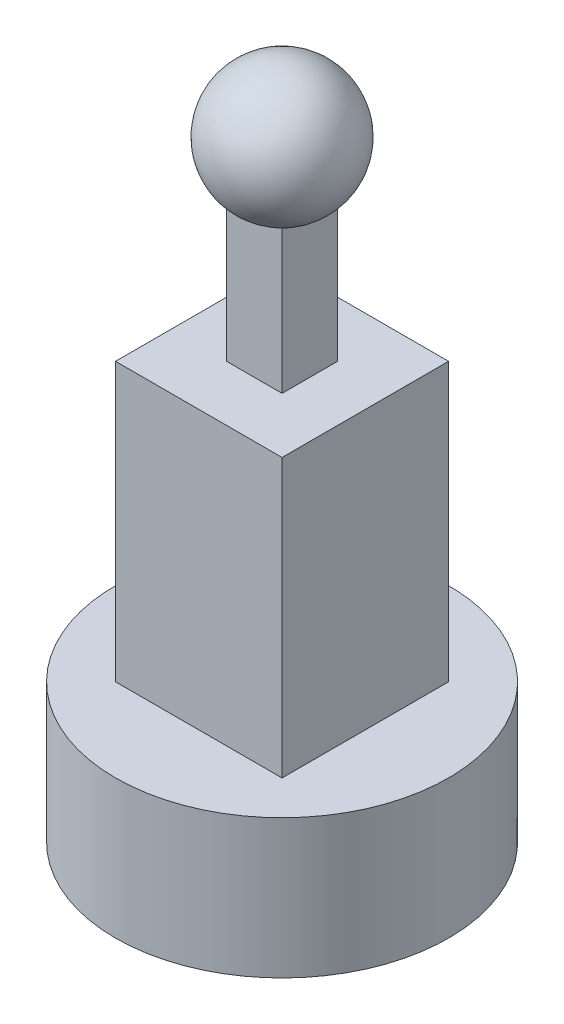
SolidWorks part; units mm, degrees
ref_plane "Front Plane" through (0, 0, 0) normal (0, 0, 1) x (1, 0, 0)
ref_plane "Top Plane" through (0, 0, 0) normal (0, 1, 0) x (1, 0, 0)
ref_plane "Right Plane" through (0, 0, 0) normal (1, 0, 0) x (0, 0, -1)
sketch "Sketch1" plane through (0, 0, 0) normal (0, 1, 0) x (1, 0, 0)
  circle A0 centre (0, 0) radius 30
  dimension "D1" = 60
extrude "Boss-Extrude1" add sketch "Sketch1" along normal blind 25
sketch "Sketch3" plane through (0, 25, 0) normal (0, 1, 0) x (1, 0, 0)
  line L0 (-15, 0.769) -> (-15, 15)
  line L1 (-15, 15) -> (15, 15)
  line L2 (15, 15) -> (15, -15)
  line L3 (15, -15) -> (-15, -15)
  line L4 (-15, -15) -> (-15, 0.769)
  dimension "D1" = 30
  dimension "D2" = 30
  dimension "D3" = 15
  dimension "D4" = 15
extrude "Boss-Extrude2" add sketch "Sketch3" along normal blind 50
sketch "Sketch4" plane through (0, 75, 0) normal (0, 1, 0) x (1, 0, 0)
  line L4 (-5, 5) -> (5, 5)
  line L5 (5, 5) -> (5, -5)
  line L6 (5, -5) -> (-5, -5)
  line L7 (-5, -5) -> (-5, 5)
  line L8 (15, 15) -> (-15, 15) construction
  line L10 (15, -15) -> (15, 15) construction
  dimension "D1" = 10
  dimension "D2" = 10
  dimension "D3" = 10
  dimension "D4" = 10
extrude "Boss-Extrude3" add sketch "Sketch4" along normal blind 30
ref_plane "Plane1" through (0, 110, 0) normal (0, 1, 0) x (1, 0, 0)
sketch "Sketch7" plane through (0, 110, 0) normal (0, 1, 0) x (1, 0, 0)
  line L0 (0, 11.606) -> (0, -11.606)
  arc A0 (0, -11.606) -> (0, 11.606) centre (0, 0) ccw
revolve "Revolve1" add sketch "Sketch7" angle 360 about L0
